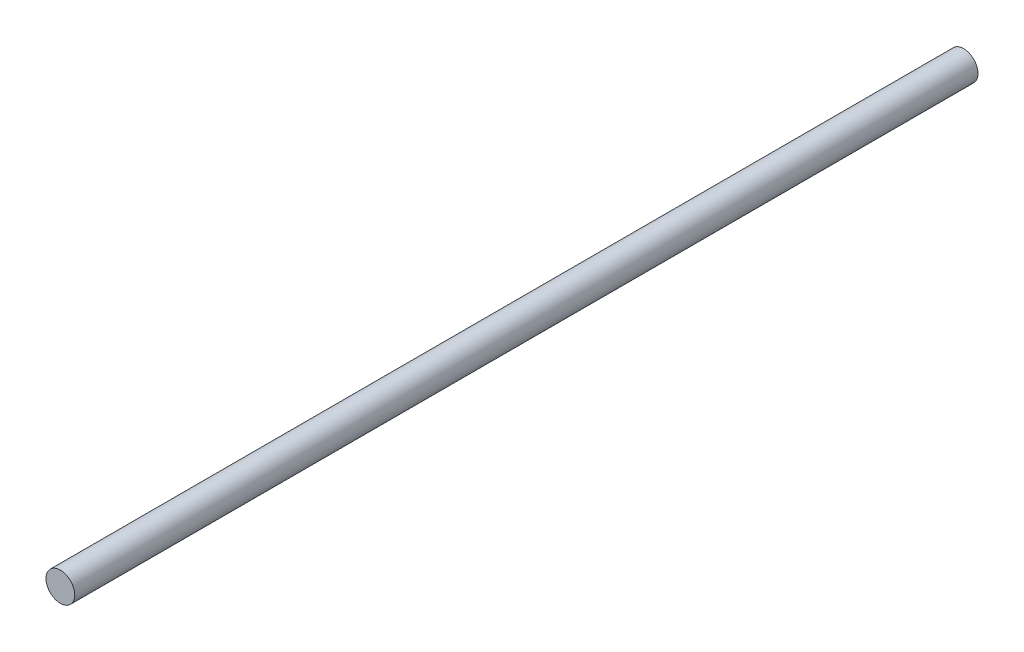
SolidWorks part; units mm, degrees
ref_plane "Front Plane" through (0, 0, 0) normal (0, 0, 1) x (1, 0, 0)
ref_plane "Top Plane" through (0, 0, 0) normal (0, 1, 0) x (1, 0, 0)
ref_plane "Right Plane" through (0, 0, 0) normal (1, 0, 0) x (0, 0, -1)
sketch "Sketch1" plane through (0, 0, 0) normal (0, 0, 1) x (1, 0, 0)
  circle A0 centre (0, 0) radius 5.1
extrude "Boss-Extrude1" add sketch "Sketch1" along normal blind 320
